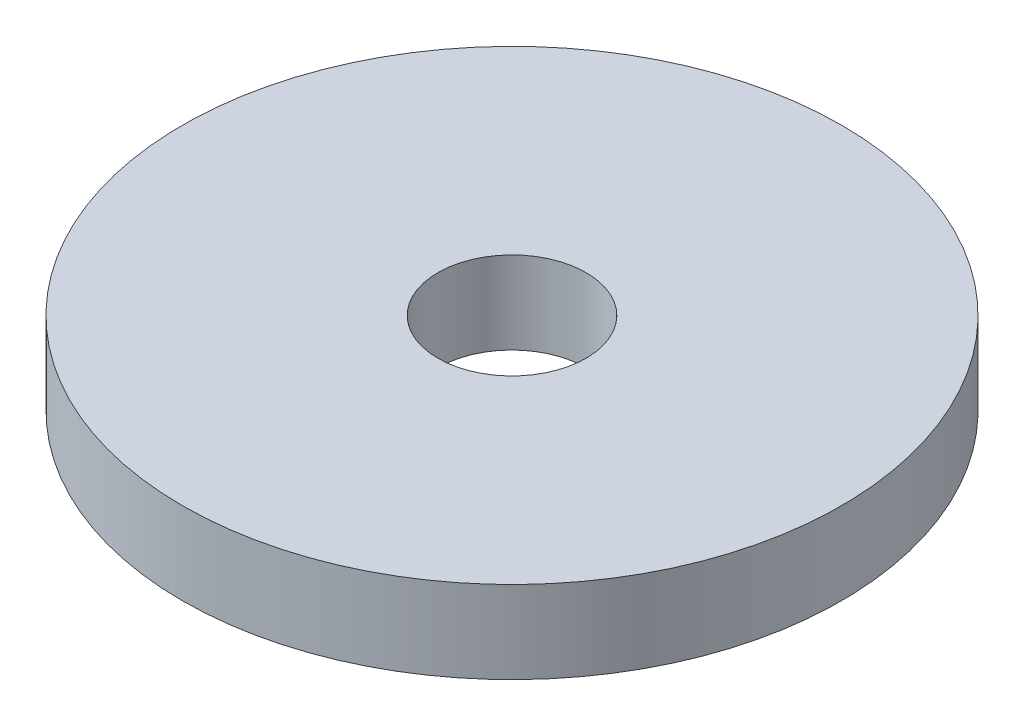
SolidWorks part; units mm, degrees
ref_plane "Front Plane" through (0, 0, 0) normal (0, 0, 1) x (1, 0, 0)
ref_plane "Top Plane" through (0, 0, 0) normal (0, 1, 0) x (1, 0, 0)
ref_plane "Right Plane" through (0, 0, 0) normal (1, 0, 0) x (0, 0, -1)
sketch "Sketch1" plane through (0, 0, 0) normal (0, 1, 0) x (1, 0, 0)
  circle A0 centre (0, 0) radius 4.5
  circle A1 centre (0, 0) radius 20
  dimension "D1" = 40
  dimension "D2" = 9
extrude "Boss-Extrude1" add sketch "Sketch1" along normal blind 5
